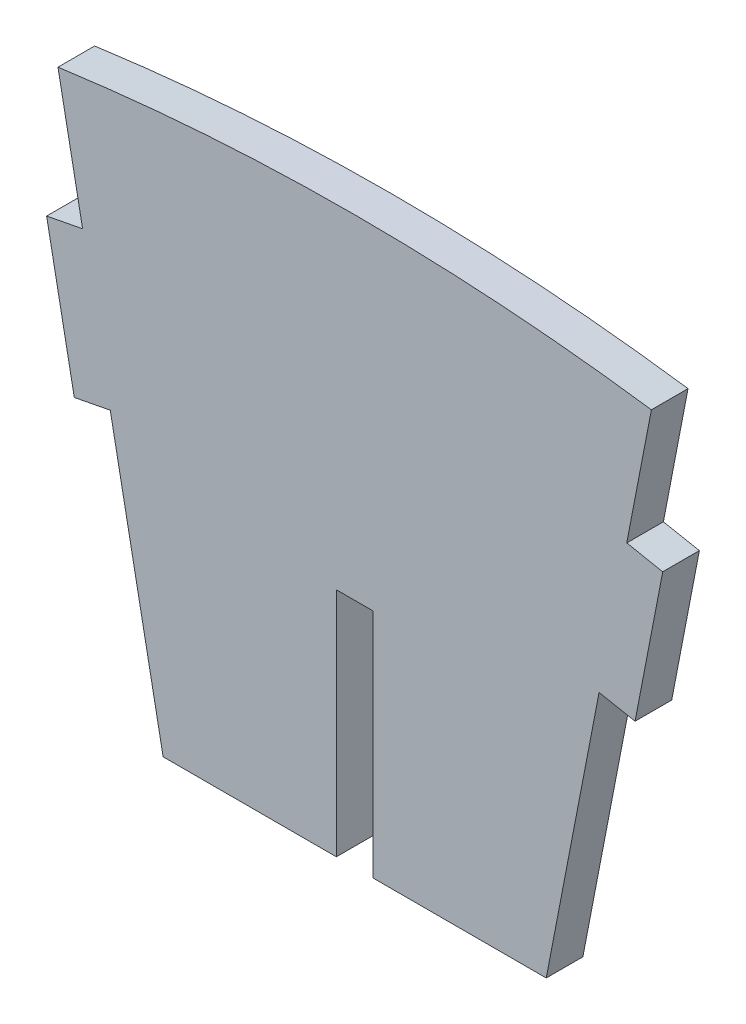
SolidWorks part; units mm, degrees
ref_plane "Front Plane" through (0, 0, 0) normal (0, 0, 1) x (1, 0, 0)
ref_plane "Top Plane" through (0, 0, 0) normal (0, 1, 0) x (1, 0, 0)
ref_plane "Right Plane" through (0, 0, 0) normal (1, 0, 0) x (0, 0, -1)
sketch "Sketch1" plane through (0, 0, 0) normal (0, 0, 1) x (1, 0, 0)
  line L0 (0.0854, 8.7656) -> (0.0854, -0.8531)
  line L1 (0.8474, 22.1096) -> (0.8474, 35.354) construction
  line L2 (1.6094, 8.7656) -> (1.6094, -0.8531)
  line L3 (8.8134, -0.8531) -> (1.6094, -0.8531)
  line L4 (8.8134, -0.8531) -> (11.0112, 10.5301)
  line L5 (11.0112, 10.5301) -> (12.5076, 10.2412)
  line L6 (12.5076, 10.2412) -> (13.6582, 16.2005)
  line L7 (13.6582, 16.2005) -> (12.1618, 16.4894)
  line L8 (12.1618, 16.4894) -> (13.0136, 20.901)
  line L9 (1.6094, 22.1096) -> (0.0854, 22.1096) construction
  line L10 (0.0854, 8.7656) -> (1.6094, 8.7656)
  line L11 (-10.467, 16.4894) -> (-11.3188, 20.901)
  line L12 (-11.9634, 16.2005) -> (-10.467, 16.4894)
  line L13 (-10.8128, 10.2412) -> (-11.9634, 16.2005)
  line L14 (-9.3164, 10.5301) -> (-10.8128, 10.2412)
  line L15 (-7.1186, -0.8531) -> (-9.3164, 10.5301)
  line L16 (0.0854, -0.8531) -> (-7.1186, -0.8531)
  line L17 (13.0136, 20.901) -> (13.1867, 21.7977)
  line L18 (-11.3188, 20.901) -> (-11.4919, 21.7977)
  line L19 (0.8474, 24.7588) -> (3.931, 24.7588) construction
  line L20 (0.8474, 8.7656) -> (0.8474, -2.4325) construction
  line L21 (0.0854, 8.7656) -> (0.0854, -2.4325) construction
  line L22 (1.6094, 8.7656) -> (1.6094, -2.4325) construction
  arc A0 (11.5749, 21.2378) -> (1.6094, 22.1096) centre (3.1054, -18.1801) ccw construction
  arc A1 (-11.3188, 20.901) -> (0.0854, 22.1096) centre (-1.4106, -18.1801) cw construction
  arc A3 (-11.4919, 21.7977) -> (13.1867, 21.7977) centre (0.8474, -66.775) cw
  dimension "D1" = 6.0693
  dimension "D2" = 1.524
  dimension "D3" = 0.762
  dimension "D4" = 0.762
extrude "Boss-Extrude1" add sketch "Sketch1" along normal blind 1.524
